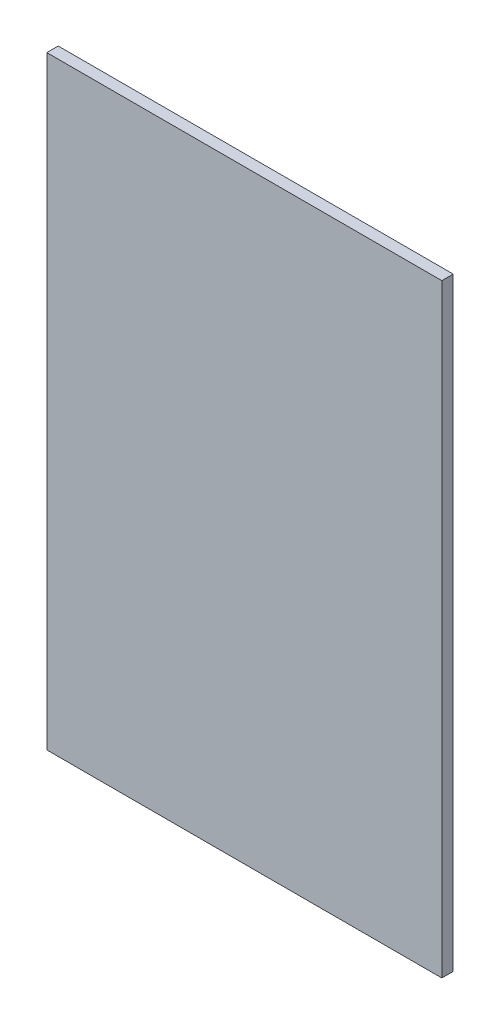
SolidWorks part; units mm, degrees
ref_plane "Plan de face" through (0, 0, 0) normal (0, 0, 1) x (1, 0, 0)
ref_plane "Plan de dessus" through (0, 0, 0) normal (0, 1, 0) x (1, 0, 0)
ref_plane "Plan de droite" through (0, 0, 0) normal (1, 0, 0) x (0, 0, -1)
sketch "Esquisse1" plane through (0, 0, 0) normal (0, 0, 1) x (1, 0, 0)
  line L0 (215.9475, 0) -> (-166.3109, 0) construction
  line L1 (-38.0708, 159) -> (169.9292, 159)
  line L2 (-38.0708, 159) -> (-38.0708, -159)
  line L3 (-38.0708, -159) -> (169.9292, -159)
  line L4 (169.9292, 159) -> (169.9292, -159)
  dimension "D1" = 318
  dimension "D2" = 208
  dimension "D3" = 159
extrude "Boss.-Extru.1" add sketch "Esquisse1" along normal blind 6
sketch "Esquisse2" plane through (0, 0, 6) normal (0, 0, 1) x (1, 0, 0)
  line L1 (208.9138, 0) -> (-120.6697, 0) construction
  line L2 (33.0441, 153) -> (88.2055, 153)
  line L3 (33.0441, 153) -> (33.0441, 145)
  line L4 (33.0441, 145) -> (88.2055, 145)
  line L5 (169.9292, 159) -> (-38.0708, 159) construction
  line L17 (88.2055, 153) -> (88.2055, 145)
  line L18 (33.0441, 125) -> (88.2055, 125)
  line L19 (33.0441, 125) -> (33.0441, 93)
  line L20 (33.0441, 93) -> (88.2055, 93)
  line L21 (88.2055, 125) -> (88.2055, 93)
  dimension "D1" = 6
  dimension "D2" = 20
  dimension "D3" = 8
  dimension "D4" = 32
  dimension "D5" = 93
